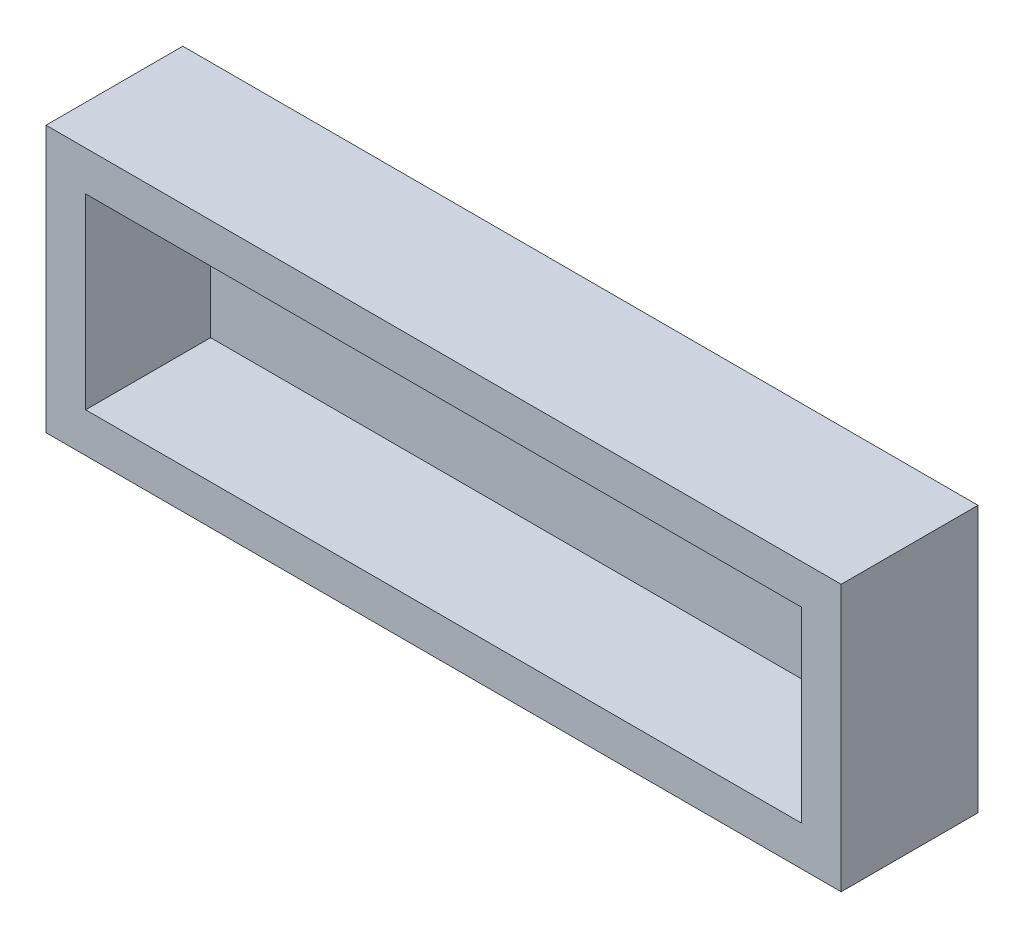
SolidWorks part; units mm, degrees
ref_plane "Front Plane" through (0, 0, 0) normal (0, 0, 1) x (1, 0, 0)
ref_plane "Top Plane" through (0, 0, 0) normal (0, 1, 0) x (1, 0, 0)
ref_plane "Right Plane" through (0, 0, 0) normal (1, 0, 0) x (0, 0, -1)
sketch "草图1" plane through (0, 0, 0) normal (0, 0, 1) x (1, 0, 0)
  line L1 (100.251, -33.576) -> (-100.251, -33.576)
  line L2 (100.251, -33.576) -> (100.251, 33.576)
  line L3 (100.251, 33.576) -> (-100.251, 33.576)
  line L4 (-100.251, -33.576) -> (-100.251, 33.576)
  line L5 (100.251, -33.576) -> (-100.251, 33.576) construction
  line L6 (100.251, 33.576) -> (-100.251, -33.576) construction
  point P0 (0, 0)
  dimension "D1" = 67.152
  dimension "D2" = 200.502
extrude "凸台-拉伸2" add sketch "草图1" along normal blind 34.5
shell "抽壳3" thickness 3
